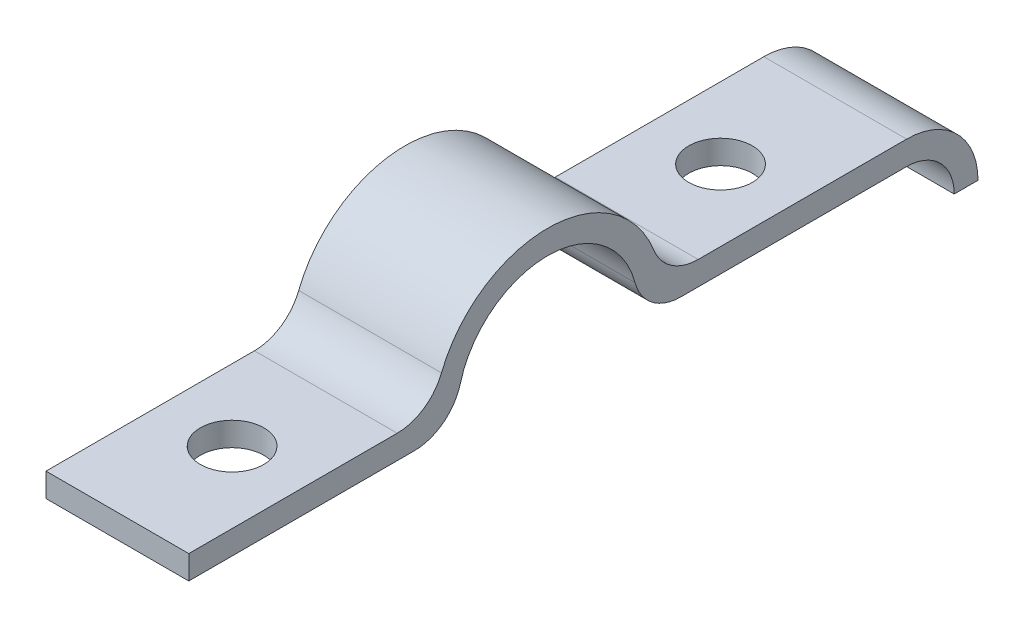
SolidWorks part; units mm, degrees
material "Brass"
ref_plane "Front Plane" through (0, 0, 0) normal (0, 0, 1) x (1, 0, 0)
ref_plane "Top Plane" through (0, 0, 0) normal (0, 1, 0) x (1, 0, 0)
ref_plane "Right Plane" through (0, 0, 0) normal (1, 0, 0) x (0, 0, -1)
sketch "Sketch2" plane through (0, 0, 0) normal (1, 0, 0) x (0, 0, -1)
  line L0 (21.6967, -3.175) -> (22.9667, -3.175)
  line L1 (19.1567, -0.635) -> (7.1154, -0.635)
  line L3 (19.1567, 0.635) -> (8.0312, 0.635)
  line L4 (-19.1567, -0.635) -> (-19.1567, 0.635)
  line L5 (19.1567, -0.635) -> (-19.1567, 0.635) construction
  line L6 (19.1567, 0.635) -> (-19.1567, -0.635) construction
  line L7 (-7.1154, -0.635) -> (-19.1567, -0.635)
  line L8 (-8.0312, 0.635) -> (-19.1567, 0.635)
  arc A0 (22.9667, -3.175) -> (19.1567, 0.635) centre (19.1567, -3.175) ccw
  arc A1 (21.6967, -3.175) -> (19.1567, -0.635) centre (19.1567, -3.175) ccw
  arc A2 (-4.6618, 1.2481) -> (-7.1154, -0.635) centre (-7.1154, 1.905) cw
  arc A3 (4.6618, 1.2481) -> (-4.6618, 1.2481) centre (0, 0) ccw
  arc A5 (5.6691, 2.2412) -> (-5.6691, 2.2412) centre (0, 0) ccw
  arc A6 (4.6618, 1.2481) -> (7.1154, -0.635) centre (7.1154, 1.905) ccw
  arc A7 (8.0312, 0.635) -> (5.6691, 2.2412) centre (8.0312, 3.175) cw
  arc A8 (-8.0312, 0.635) -> (-5.6691, 2.2412) centre (-8.0312, 3.175) ccw
  point P0 (0, 0)
  point P6 (-19.1567, 0)
  point P13 (-4.784, -0.635)
  dimension "D3" = 5.08
  dimension "D4" = 9.652
  dimension "D5" = 2.54
  dimension "D1" = 1.27
  dimension "D2" = 19.1567
extrude "Boss-Extrude1" add sketch "Sketch2" along normal mid plane 7.62
sketch "Sketch3" plane through (0, 0.635, 0) normal (0, 1, 0) x (1, 0, 0)
  circle A0 centre (0, 13.0353) radius 1.6948
  circle A1 centre (0, -13.0353) radius 1.6948
  dimension "D1" = 13.0353
  dimension "D2" = 13.0353
extrude "Cut-Extrude1" cut sketch "Sketch3" against normal up to next
equation "\"D2@Sketch3\"=\"D1@Sketch3\""
